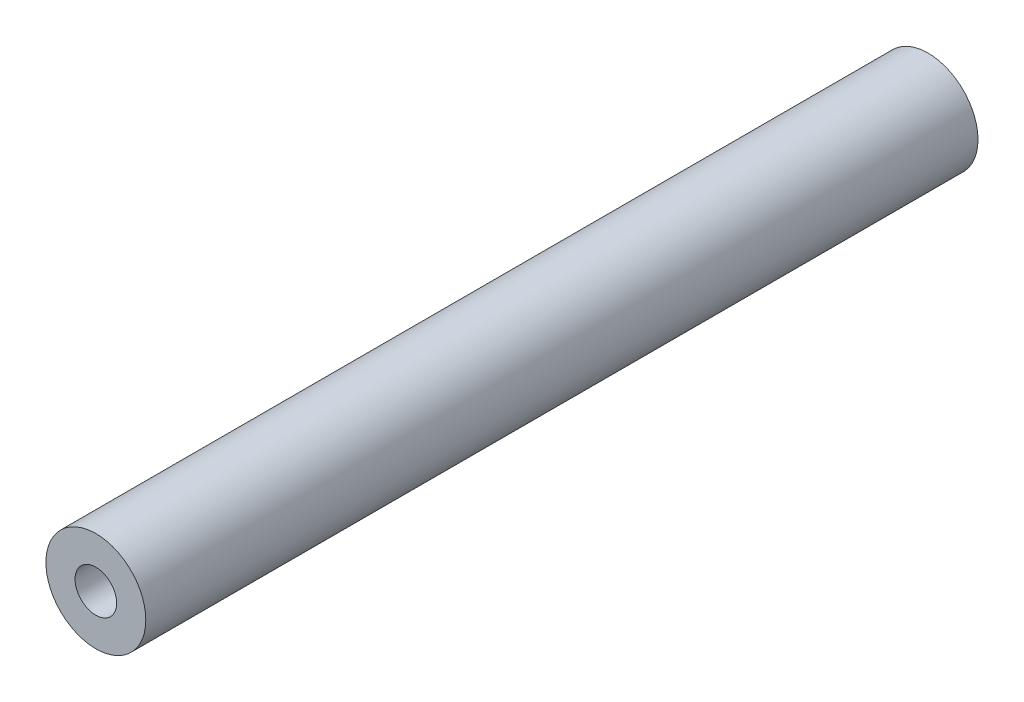
SolidWorks part; units mm, degrees
ref_plane "前视基准面" through (0, 0, 0) normal (0, 0, 1) x (1, 0, 0)
ref_plane "上视基准面" through (0, 0, 0) normal (0, 1, 0) x (1, 0, 0)
ref_plane "右视基准面" through (0, 0, 0) normal (1, 0, 0) x (0, 0, -1)
sketch "草图1" plane through (0, 0, 0) normal (0, 0, 1) x (1, 0, 0)
  circle A0 centre (0, 0) radius 6
  dimension "D1" = 12
extrude "凸台-拉伸1" add sketch "草图1" along normal blind 100
hole_wizard "M6 螺纹孔1" positions "草图2" profile "草图3" tap size "M6" standard "ISO"
sketch "草图2" plane through (0, 0, 0) normal (0, 0, -1) x (-1, 0, 0)
  point P0 (0, 0)
sketch "草图3" plane through (0, 0, 0) normal (1, 0, 0) x (0, 1, 0)
  line L0 (0, 0) -> (0, 16.5022)
  line L1 (0, 16.5022) -> (2.5, 15)
  line L2 (2.5, 15) -> (2.5, 0)
  line L5 (2.5, 0) -> (0, 0)
  line L10 (0, 16.5022) -> (-2.5, 15) construction
  line L11 (0, -6.35) -> (0, 107.95) construction
  dimension "螺纹孔钻头直径" = 5
  dimension "螺纹孔钻头深度" = 15
  dimension "导头角度" = 118
cosmetic thread "孔螺蚊线1"
hole_wizard "M6 螺纹孔2" positions "草图4" profile "草图5" tap size "M6" standard "ISO"
sketch "草图4" plane through (0, 0, 100) normal (0, 0, 1) x (1, 0, 0)
  point P0 (0, 0)
sketch "草图5" plane through (0, 0, 100) normal (1, 0, 0) x (0, -1, 0)
  line L0 (0, 0) -> (0, 16.5022)
  line L1 (0, 16.5022) -> (2.5, 15)
  line L2 (2.5, 15) -> (2.5, 0)
  line L5 (2.5, 0) -> (0, 0)
  line L10 (0, 16.5022) -> (-2.5, 15) construction
  line L11 (0, -6.35) -> (0, 107.95) construction
  dimension "螺纹孔钻头直径" = 5
  dimension "螺纹孔钻头深度" = 15
  dimension "导头角度" = 118
cosmetic thread "孔螺蚊线2" parameters "D1"=12, "D2"=6
